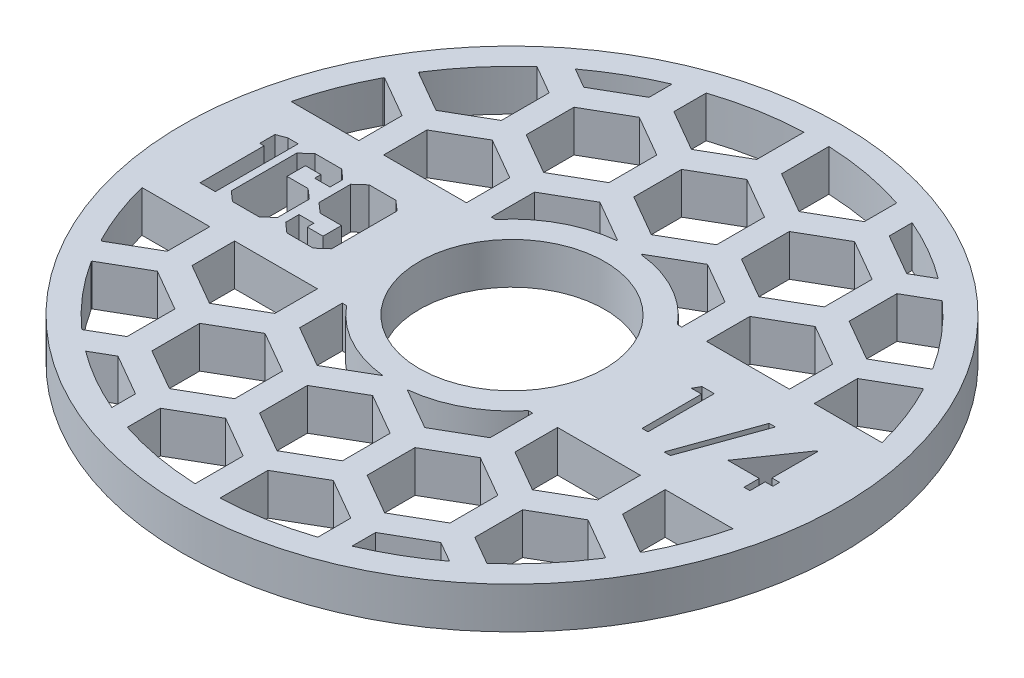
SolidWorks part; units mm, degrees
ref_plane "Front Plane" through (0, 0, 0) normal (0, 0, 1) x (1, 0, 0)
ref_plane "Top Plane" through (0, 0, 0) normal (0, 1, 0) x (1, 0, 0)
ref_plane "Right Plane" through (0, 0, 0) normal (1, 0, 0) x (0, 0, -1)
sketch "Sketch1" plane through (0, 0, 0) normal (0, 1, 0) x (1, 0, 0)
  circle A0 centre (0, 0) radius 14.224
  circle A1 centre (0, 0) radius 50.546
  dimension "D1" = 28.448
  dimension "D2" = 101.092
extrude "Boss-Extrude1" add sketch "Sketch1" along normal blind 6.35
sketch "Sketch2" plane through (0, 6.35, 0) normal (0, 1, 0) x (1, 0, 0)
  line L0 (-14.224, 0) -> (-50.546, 0) construction
  line L1 (-14.224, -6.35) -> (-50.546, -6.35) construction
  line L2 (14.224, 0) -> (50.546, 0) construction
  line L3 (14.224, -5.08) -> (50.546, -5.08) construction
  circle A0 centre (0, 0) radius 14.224 construction
  circle A1 centre (0, 0) radius 50.546 construction
  text T0 "169" font "Jersey M54" height 12.7
  text T1 "1/4" font "Century Gothic" height 10.16
  dimension "D1" = 6.35
  dimension "D2" = 5.08
extrude "Cut-Extrude1" cut sketch "Sketch2" against normal through all both and the other way through all
sketch "Sketch3" plane through (0, 6.35, 0) normal (0, 1, 0) x (1, 0, 0)
  line L0 (0, 11.43) -> (0, -11.43)
  line L1 (-49.2367, 11.43) -> (49.2367, 11.43)
  line L2 (-49.2367, -11.43) -> (49.2367, -11.43)
  line L3 (16.51, -7.3323) -> (22.86, -3.6662)
  line L4 (0, -7.3323) -> (6.35, -3.6662)
  line L5 (6.35, -3.6662) -> (6.35, 3.6662)
  line L6 (6.35, 3.6662) -> (0, 7.3323)
  line L7 (0, 7.3323) -> (-6.35, 3.6662)
  line L8 (-6.35, 3.6662) -> (-6.35, -3.6662)
  line L9 (-6.35, -3.6662) -> (0, -7.3323)
  line L16 (8.255, -21.6304) -> (14.605, -17.9643)
  line L17 (14.605, -17.9643) -> (14.605, -10.6319)
  line L18 (14.605, -10.6319) -> (8.255, -6.9657)
  line L19 (8.255, -6.9657) -> (1.905, -10.6319)
  line L20 (1.905, -10.6319) -> (1.905, -17.9643)
  line L21 (1.905, -17.9643) -> (8.255, -21.6304)
  line L22 (22.86, -3.6662) -> (22.86, 3.6662)
  line L23 (22.86, 3.6662) -> (16.51, 7.3323)
  line L24 (16.51, 7.3323) -> (10.16, 3.6662)
  line L25 (10.16, 3.6662) -> (10.16, -3.6662)
  line L26 (10.16, -3.6662) -> (16.51, -7.3323)
  line L27 (24.765, -21.6304) -> (31.115, -17.9643)
  line L28 (31.115, -17.9643) -> (31.115, -10.6319)
  line L29 (31.115, -10.6319) -> (24.765, -6.9657)
  line L30 (24.765, -6.9657) -> (18.415, -10.6319)
  line L31 (18.415, -10.6319) -> (18.415, -17.9643)
  line L32 (18.415, -17.9643) -> (24.765, -21.6304)
  line L33 (33.02, -7.3323) -> (39.37, -3.6662)
  line L34 (39.37, -3.6662) -> (39.37, 3.6662)
  line L35 (39.37, 3.6662) -> (33.02, 7.3323)
  line L36 (33.02, 7.3323) -> (26.67, 3.6662)
  line L37 (26.67, 3.6662) -> (26.67, -3.6662)
  line L38 (26.67, -3.6662) -> (33.02, -7.3323)
  line L39 (41.275, -21.6304) -> (47.625, -17.9643)
  line L40 (47.625, -17.9643) -> (47.625, -10.6319)
  line L41 (47.625, -10.6319) -> (41.275, -6.9657)
  line L42 (41.275, -6.9657) -> (34.925, -10.6319)
  line L43 (34.925, -10.6319) -> (34.925, -17.9643)
  line L44 (34.925, -17.9643) -> (41.275, -21.6304)
  line L45 (49.53, -7.3323) -> (55.88, -3.6662)
  line L46 (55.88, -3.6662) -> (55.88, 3.6662)
  line L47 (55.88, 3.6662) -> (49.53, 7.3323)
  line L48 (49.53, 7.3323) -> (43.18, 3.6662)
  line L49 (43.18, 3.6662) -> (43.18, -3.6662)
  line L50 (43.18, -3.6662) -> (49.53, -7.3323)
  line L51 (57.785, -21.6304) -> (64.135, -17.9643)
  line L52 (64.135, -17.9643) -> (64.135, -10.6319)
  line L53 (64.135, -10.6319) -> (57.785, -6.9657)
  line L54 (57.785, -6.9657) -> (51.435, -10.6319)
  line L55 (51.435, -10.6319) -> (51.435, -17.9643)
  line L56 (51.435, -17.9643) -> (57.785, -21.6304)
  line L57 (-16.51, -7.3323) -> (-10.16, -3.6662)
  line L58 (-10.16, -3.6662) -> (-10.16, 3.6662)
  line L59 (-10.16, 3.6662) -> (-16.51, 7.3323)
  line L60 (-16.51, 7.3323) -> (-22.86, 3.6662)
  line L61 (-22.86, 3.6662) -> (-22.86, -3.6662)
  line L62 (-22.86, -3.6662) -> (-16.51, -7.3323)
  line L63 (-8.255, -21.6304) -> (-1.905, -17.9643)
  line L64 (-1.905, -17.9643) -> (-1.905, -10.6319)
  line L65 (-1.905, -10.6319) -> (-8.255, -6.9657)
  line L66 (-8.255, -6.9657) -> (-14.605, -10.6319)
  line L67 (-14.605, -10.6319) -> (-14.605, -17.9643)
  line L68 (-14.605, -17.9643) -> (-8.255, -21.6304)
  line L69 (-33.02, -7.3323) -> (-26.67, -3.6662)
  line L70 (-26.67, -3.6662) -> (-26.67, 3.6662)
  line L71 (-26.67, 3.6662) -> (-33.02, 7.3323)
  line L72 (-33.02, 7.3323) -> (-39.37, 3.6662)
  line L73 (-39.37, 3.6662) -> (-39.37, -3.6662)
  line L74 (-39.37, -3.6662) -> (-33.02, -7.3323)
  line L75 (-24.765, -21.6304) -> (-18.415, -17.9643)
  line L76 (-18.415, -17.9643) -> (-18.415, -10.6319)
  line L77 (-18.415, -10.6319) -> (-24.765, -6.9657)
  line L78 (-24.765, -6.9657) -> (-31.115, -10.6319)
  line L79 (-31.115, -10.6319) -> (-31.115, -17.9643)
  line L80 (-31.115, -17.9643) -> (-24.765, -21.6304)
  line L81 (-49.53, -7.3323) -> (-43.18, -3.6662)
  line L82 (-43.18, -3.6662) -> (-43.18, 3.6662)
  line L83 (-43.18, 3.6662) -> (-49.53, 7.3323)
  line L84 (-49.53, 7.3323) -> (-55.88, 3.6662)
  line L85 (-55.88, 3.6662) -> (-55.88, -3.6662)
  line L86 (-55.88, -3.6662) -> (-49.53, -7.3323)
  line L87 (-41.275, -21.6304) -> (-34.925, -17.9643)
  line L88 (-34.925, -17.9643) -> (-34.925, -10.6319)
  line L89 (-34.925, -10.6319) -> (-41.275, -6.9657)
  line L90 (-41.275, -6.9657) -> (-47.625, -10.6319)
  line L91 (-47.625, -10.6319) -> (-47.625, -17.9643)
  line L92 (-47.625, -17.9643) -> (-41.275, -21.6304)
  line L93 (-49.53, 21.3697) -> (-43.18, 25.0358)
  line L94 (-43.18, 25.0358) -> (-43.18, 32.3682)
  line L95 (-43.18, 32.3682) -> (-49.53, 36.0343)
  line L96 (-49.53, 36.0343) -> (-55.88, 32.3682)
  line L97 (-55.88, 32.3682) -> (-55.88, 25.0358)
  line L98 (-55.88, 25.0358) -> (-49.53, 21.3697)
  line L99 (-41.275, 7.0716) -> (-34.925, 10.7377)
  line L100 (-34.925, 10.7377) -> (-34.925, 18.0701)
  line L101 (-34.925, 18.0701) -> (-41.275, 21.7363)
  line L102 (-41.275, 21.7363) -> (-47.625, 18.0701)
  line L103 (-47.625, 18.0701) -> (-47.625, 10.7377)
  line L104 (-47.625, 10.7377) -> (-41.275, 7.0716)
  line L105 (-33.02, 21.3697) -> (-26.67, 25.0358)
  line L106 (-26.67, 25.0358) -> (-26.67, 32.3682)
  line L107 (-26.67, 32.3682) -> (-33.02, 36.0343)
  line L108 (-33.02, 36.0343) -> (-39.37, 32.3682)
  line L109 (-39.37, 32.3682) -> (-39.37, 25.0358)
  line L110 (-39.37, 25.0358) -> (-33.02, 21.3697)
  line L111 (-24.765, 7.0716) -> (-18.415, 10.7377)
  line L112 (-18.415, 10.7377) -> (-18.415, 18.0701)
  line L113 (-18.415, 18.0701) -> (-24.765, 21.7363)
  line L114 (-24.765, 21.7363) -> (-31.115, 18.0701)
  line L115 (-31.115, 18.0701) -> (-31.115, 10.7377)
  line L116 (-31.115, 10.7377) -> (-24.765, 7.0716)
  line L117 (-16.51, 21.3697) -> (-10.16, 25.0358)
  line L118 (-10.16, 25.0358) -> (-10.16, 32.3682)
  line L119 (-10.16, 32.3682) -> (-16.51, 36.0343)
  line L120 (-16.51, 36.0343) -> (-22.86, 32.3682)
  line L121 (-22.86, 32.3682) -> (-22.86, 25.0358)
  line L122 (-22.86, 25.0358) -> (-16.51, 21.3697)
  line L123 (-8.255, 7.0716) -> (-1.905, 10.7377)
  line L124 (-1.905, 10.7377) -> (-1.905, 18.0701)
  line L125 (-1.905, 18.0701) -> (-8.255, 21.7363)
  line L126 (-8.255, 21.7363) -> (-14.605, 18.0701)
  line L127 (-14.605, 18.0701) -> (-14.605, 10.7377)
  line L128 (-14.605, 10.7377) -> (-8.255, 7.0716)
  line L129 (0, 21.3697) -> (6.35, 25.0358)
  line L130 (6.35, 25.0358) -> (6.35, 32.3682)
  line L131 (6.35, 32.3682) -> (0, 36.0343)
  line L132 (0, 36.0343) -> (-6.35, 32.3682)
  line L133 (-6.35, 32.3682) -> (-6.35, 25.0358)
  line L134 (-6.35, 25.0358) -> (0, 21.3697)
  line L135 (8.255, 7.0716) -> (14.605, 10.7377)
  line L136 (14.605, 10.7377) -> (14.605, 18.0701)
  line L137 (14.605, 18.0701) -> (8.255, 21.7363)
  line L138 (8.255, 21.7363) -> (1.905, 18.0701)
  line L139 (1.905, 18.0701) -> (1.905, 10.7377)
  line L140 (1.905, 10.7377) -> (8.255, 7.0716)
  line L141 (16.51, 21.3697) -> (22.86, 25.0358)
  line L142 (22.86, 25.0358) -> (22.86, 32.3682)
  line L143 (22.86, 32.3682) -> (16.51, 36.0343)
  line L144 (16.51, 36.0343) -> (10.16, 32.3682)
  line L145 (10.16, 32.3682) -> (10.16, 25.0358)
  line L146 (10.16, 25.0358) -> (16.51, 21.3697)
  line L147 (24.765, 7.0716) -> (31.115, 10.7377)
  line L148 (31.115, 10.7377) -> (31.115, 18.0701)
  line L149 (31.115, 18.0701) -> (24.765, 21.7363)
  line L150 (24.765, 21.7363) -> (18.415, 18.0701)
  line L151 (18.415, 18.0701) -> (18.415, 10.7377)
  line L152 (18.415, 10.7377) -> (24.765, 7.0716)
  line L153 (33.02, 21.3697) -> (39.37, 25.0358)
  line L154 (39.37, 25.0358) -> (39.37, 32.3682)
  line L155 (39.37, 32.3682) -> (33.02, 36.0343)
  line L156 (33.02, 36.0343) -> (26.67, 32.3682)
  line L157 (26.67, 32.3682) -> (26.67, 25.0358)
  line L158 (26.67, 25.0358) -> (33.02, 21.3697)
  line L159 (41.275, 7.0716) -> (47.625, 10.7377)
  line L160 (47.625, 10.7377) -> (47.625, 18.0701)
  line L161 (47.625, 18.0701) -> (41.275, 21.7363)
  line L162 (41.275, 21.7363) -> (34.925, 18.0701)
  line L163 (34.925, 18.0701) -> (34.925, 10.7377)
  line L164 (34.925, 10.7377) -> (41.275, 7.0716)
  line L165 (49.53, 21.3697) -> (55.88, 25.0358)
  line L166 (55.88, 25.0358) -> (55.88, 32.3682)
  line L167 (55.88, 32.3682) -> (49.53, 36.0343)
  line L168 (49.53, 36.0343) -> (43.18, 32.3682)
  line L169 (43.18, 32.3682) -> (43.18, 25.0358)
  line L170 (43.18, 25.0358) -> (49.53, 21.3697)
  line L171 (57.785, 7.0716) -> (64.135, 10.7377)
  line L172 (64.135, 10.7377) -> (64.135, 18.0701)
  line L173 (64.135, 18.0701) -> (57.785, 21.7363)
  line L174 (57.785, 21.7363) -> (51.435, 18.0701)
  line L175 (51.435, 18.0701) -> (51.435, 10.7377)
  line L176 (51.435, 10.7377) -> (57.785, 7.0716)
  line L177 (-49.53, 50.0717) -> (-43.18, 53.7378)
  line L178 (-43.18, 53.7378) -> (-43.18, 61.0702)
  line L179 (-43.18, 61.0702) -> (-49.53, 64.7363)
  line L180 (-49.53, 64.7363) -> (-55.88, 61.0702)
  line L181 (-55.88, 61.0702) -> (-55.88, 53.7378)
  line L182 (-55.88, 53.7378) -> (-49.53, 50.0717)
  line L183 (-41.275, 35.7736) -> (-34.925, 39.4397)
  line L184 (-34.925, 39.4397) -> (-34.925, 46.7721)
  line L185 (-34.925, 46.7721) -> (-41.275, 50.4383)
  line L186 (-41.275, 50.4383) -> (-47.625, 46.7721)
  line L187 (-47.625, 46.7721) -> (-47.625, 39.4397)
  line L188 (-47.625, 39.4397) -> (-41.275, 35.7736)
  line L189 (-33.02, 50.0717) -> (-26.67, 53.7378)
  line L190 (-26.67, 53.7378) -> (-26.67, 61.0702)
  line L191 (-26.67, 61.0702) -> (-33.02, 64.7363)
  line L192 (-33.02, 64.7363) -> (-39.37, 61.0702)
  line L193 (-39.37, 61.0702) -> (-39.37, 53.7378)
  line L194 (-39.37, 53.7378) -> (-33.02, 50.0717)
  line L195 (-24.765, 35.7736) -> (-18.415, 39.4397)
  line L196 (-18.415, 39.4397) -> (-18.415, 46.7721)
  line L197 (-18.415, 46.7721) -> (-24.765, 50.4383)
  line L198 (-24.765, 50.4383) -> (-31.115, 46.7721)
  line L199 (-31.115, 46.7721) -> (-31.115, 39.4397)
  line L200 (-31.115, 39.4397) -> (-24.765, 35.7736)
  line L201 (-16.51, 50.0717) -> (-10.16, 53.7378)
  line L202 (-10.16, 53.7378) -> (-10.16, 61.0702)
  line L203 (-10.16, 61.0702) -> (-16.51, 64.7363)
  line L204 (-16.51, 64.7363) -> (-22.86, 61.0702)
  line L205 (-22.86, 61.0702) -> (-22.86, 53.7378)
  line L206 (-22.86, 53.7378) -> (-16.51, 50.0717)
  line L207 (-8.255, 35.7736) -> (-1.905, 39.4397)
  line L208 (-1.905, 39.4397) -> (-1.905, 46.7721)
  line L209 (-1.905, 46.7721) -> (-8.255, 50.4383)
  line L210 (-8.255, 50.4383) -> (-14.605, 46.7721)
  line L211 (-14.605, 46.7721) -> (-14.605, 39.4397)
  line L212 (-14.605, 39.4397) -> (-8.255, 35.7736)
  line L213 (0, 50.0717) -> (6.35, 53.7378)
  line L214 (6.35, 53.7378) -> (6.35, 61.0702)
  line L215 (6.35, 61.0702) -> (0, 64.7363)
  line L216 (0, 64.7363) -> (-6.35, 61.0702)
  line L217 (-6.35, 61.0702) -> (-6.35, 53.7378)
  line L218 (-6.35, 53.7378) -> (0, 50.0717)
  line L219 (8.255, 35.7736) -> (14.605, 39.4397)
  line L220 (14.605, 39.4397) -> (14.605, 46.7721)
  line L221 (14.605, 46.7721) -> (8.255, 50.4383)
  line L222 (8.255, 50.4383) -> (1.905, 46.7721)
  line L223 (1.905, 46.7721) -> (1.905, 39.4397)
  line L224 (1.905, 39.4397) -> (8.255, 35.7736)
  line L225 (16.51, 50.0717) -> (22.86, 53.7378)
  line L226 (22.86, 53.7378) -> (22.86, 61.0702)
  line L227 (22.86, 61.0702) -> (16.51, 64.7363)
  line L228 (16.51, 64.7363) -> (10.16, 61.0702)
  line L229 (10.16, 61.0702) -> (10.16, 53.7378)
  line L230 (10.16, 53.7378) -> (16.51, 50.0717)
  line L231 (24.765, 35.7736) -> (31.115, 39.4397)
  line L232 (31.115, 39.4397) -> (31.115, 46.7721)
  line L233 (31.115, 46.7721) -> (24.765, 50.4383)
  line L234 (24.765, 50.4383) -> (18.415, 46.7721)
  line L235 (18.415, 46.7721) -> (18.415, 39.4397)
  line L236 (18.415, 39.4397) -> (24.765, 35.7736)
  line L237 (33.02, 50.0717) -> (39.37, 53.7378)
  line L238 (39.37, 53.7378) -> (39.37, 61.0702)
  line L239 (39.37, 61.0702) -> (33.02, 64.7363)
  line L240 (33.02, 64.7363) -> (26.67, 61.0702)
  line L241 (26.67, 61.0702) -> (26.67, 53.7378)
  line L242 (26.67, 53.7378) -> (33.02, 50.0717)
  line L243 (41.275, 35.7736) -> (47.625, 39.4397)
  line L244 (47.625, 39.4397) -> (47.625, 46.7721)
  line L245 (47.625, 46.7721) -> (41.275, 50.4383)
  line L246 (41.275, 50.4383) -> (34.925, 46.7721)
  line L247 (34.925, 46.7721) -> (34.925, 39.4397)
  line L248 (34.925, 39.4397) -> (41.275, 35.7736)
  line L249 (49.53, 50.0717) -> (55.88, 53.7378)
  line L250 (55.88, 53.7378) -> (55.88, 61.0702)
  line L251 (55.88, 61.0702) -> (49.53, 64.7363)
  line L252 (49.53, 64.7363) -> (43.18, 61.0702)
  line L253 (43.18, 61.0702) -> (43.18, 53.7378)
  line L254 (43.18, 53.7378) -> (49.53, 50.0717)
  line L255 (57.785, 35.7736) -> (64.135, 39.4397)
  line L256 (64.135, 39.4397) -> (64.135, 46.7721)
  line L257 (64.135, 46.7721) -> (57.785, 50.4383)
  line L258 (57.785, 50.4383) -> (51.435, 46.7721)
  line L259 (51.435, 46.7721) -> (51.435, 39.4397)
  line L260 (51.435, 39.4397) -> (57.785, 35.7736)
  line L261 (-49.53, -36.0343) -> (-43.18, -32.3682)
  line L262 (-43.18, -32.3682) -> (-43.18, -25.0358)
  line L263 (-43.18, -25.0358) -> (-49.53, -21.3697)
  line L264 (-49.53, -21.3697) -> (-55.88, -25.0358)
  line L265 (-55.88, -25.0358) -> (-55.88, -32.3682)
  line L266 (-55.88, -32.3682) -> (-49.53, -36.0343)
  line L267 (-41.275, -50.3324) -> (-34.925, -46.6663)
  line L268 (-34.925, -46.6663) -> (-34.925, -39.3339)
  line L269 (-34.925, -39.3339) -> (-41.275, -35.6677)
  line L270 (-41.275, -35.6677) -> (-47.625, -39.3339)
  line L271 (-47.625, -39.3339) -> (-47.625, -46.6663)
  line L272 (-47.625, -46.6663) -> (-41.275, -50.3324)
  line L273 (-33.02, -36.0343) -> (-26.67, -32.3682)
  line L274 (-26.67, -32.3682) -> (-26.67, -25.0358)
  line L275 (-26.67, -25.0358) -> (-33.02, -21.3697)
  line L276 (-33.02, -21.3697) -> (-39.37, -25.0358)
  line L277 (-39.37, -25.0358) -> (-39.37, -32.3682)
  line L278 (-39.37, -32.3682) -> (-33.02, -36.0343)
  line L279 (-24.765, -50.3324) -> (-18.415, -46.6663)
  line L280 (-18.415, -46.6663) -> (-18.415, -39.3339)
  line L281 (-18.415, -39.3339) -> (-24.765, -35.6677)
  line L282 (-24.765, -35.6677) -> (-31.115, -39.3339)
  line L283 (-31.115, -39.3339) -> (-31.115, -46.6663)
  line L284 (-31.115, -46.6663) -> (-24.765, -50.3324)
  line L285 (-16.51, -36.0343) -> (-10.16, -32.3682)
  line L286 (-10.16, -32.3682) -> (-10.16, -25.0358)
  line L287 (-10.16, -25.0358) -> (-16.51, -21.3697)
  line L288 (-16.51, -21.3697) -> (-22.86, -25.0358)
  line L289 (-22.86, -25.0358) -> (-22.86, -32.3682)
  line L290 (-22.86, -32.3682) -> (-16.51, -36.0343)
  line L291 (-8.255, -50.3324) -> (-1.905, -46.6663)
  line L292 (-1.905, -46.6663) -> (-1.905, -39.3339)
  line L293 (-1.905, -39.3339) -> (-8.255, -35.6677)
  line L294 (-8.255, -35.6677) -> (-14.605, -39.3339)
  line L295 (-14.605, -39.3339) -> (-14.605, -46.6663)
  line L296 (-14.605, -46.6663) -> (-8.255, -50.3324)
  line L297 (0, -36.0343) -> (6.35, -32.3682)
  line L298 (6.35, -32.3682) -> (6.35, -25.0358)
  line L299 (6.35, -25.0358) -> (0, -21.3697)
  line L300 (0, -21.3697) -> (-6.35, -25.0358)
  line L301 (-6.35, -25.0358) -> (-6.35, -32.3682)
  line L302 (-6.35, -32.3682) -> (0, -36.0343)
  line L303 (8.255, -50.3324) -> (14.605, -46.6663)
  line L304 (14.605, -46.6663) -> (14.605, -39.3339)
  line L305 (14.605, -39.3339) -> (8.255, -35.6677)
  line L306 (8.255, -35.6677) -> (1.905, -39.3339)
  line L307 (1.905, -39.3339) -> (1.905, -46.6663)
  line L308 (1.905, -46.6663) -> (8.255, -50.3324)
  line L309 (16.51, -36.0343) -> (22.86, -32.3682)
  line L310 (22.86, -32.3682) -> (22.86, -25.0358)
  line L311 (22.86, -25.0358) -> (16.51, -21.3697)
  line L312 (16.51, -21.3697) -> (10.16, -25.0358)
  line L313 (10.16, -25.0358) -> (10.16, -32.3682)
  line L314 (10.16, -32.3682) -> (16.51, -36.0343)
  line L315 (24.765, -50.3324) -> (31.115, -46.6663)
  line L316 (31.115, -46.6663) -> (31.115, -39.3339)
  line L317 (31.115, -39.3339) -> (24.765, -35.6677)
  line L318 (24.765, -35.6677) -> (18.415, -39.3339)
  line L319 (18.415, -39.3339) -> (18.415, -46.6663)
  line L320 (18.415, -46.6663) -> (24.765, -50.3324)
  line L321 (33.02, -36.0343) -> (39.37, -32.3682)
  line L322 (39.37, -32.3682) -> (39.37, -25.0358)
  line L323 (39.37, -25.0358) -> (33.02, -21.3697)
  line L324 (33.02, -21.3697) -> (26.67, -25.0358)
  line L325 (26.67, -25.0358) -> (26.67, -32.3682)
  line L326 (26.67, -32.3682) -> (33.02, -36.0343)
  line L327 (41.275, -50.3324) -> (47.625, -46.6663)
  line L328 (47.625, -46.6663) -> (47.625, -39.3339)
  line L329 (47.625, -39.3339) -> (41.275, -35.6677)
  line L330 (41.275, -35.6677) -> (34.925, -39.3339)
  line L331 (34.925, -39.3339) -> (34.925, -46.6663)
  line L332 (34.925, -46.6663) -> (41.275, -50.3324)
  line L333 (49.53, -36.0343) -> (55.88, -32.3682)
  line L334 (55.88, -32.3682) -> (55.88, -25.0358)
  line L335 (55.88, -25.0358) -> (49.53, -21.3697)
  line L336 (49.53, -21.3697) -> (43.18, -25.0358)
  line L337 (43.18, -25.0358) -> (43.18, -32.3682)
  line L338 (43.18, -32.3682) -> (49.53, -36.0343)
  line L339 (57.785, -50.3324) -> (64.135, -46.6663)
  line L340 (64.135, -46.6663) -> (64.135, -39.3339)
  line L341 (64.135, -39.3339) -> (57.785, -35.6677)
  line L342 (57.785, -35.6677) -> (51.435, -39.3339)
  line L343 (51.435, -39.3339) -> (51.435, -46.6663)
  line L344 (51.435, -46.6663) -> (57.785, -50.3324)
  circle A0 centre (0, 0) radius 50.546 construction
  circle A1 centre (0, 0) radius 18.034
  circle A2 centre (0, 0) radius 46.736
  circle A3 centre (0, 0) radius 6.35 construction
  circle A4 centre (8.255, -14.2981) radius 6.35 construction
  point P4 (0, 0)
  point P10 (0, 11.43)
  point P13 (0, -11.43)
  dimension "D2" = 36.068
  dimension "D3" = 93.472
  dimension "D1" = 22.86
  dimension "D4" = 12.7
  dimension "D5" = 12.7
  dimension "D6" = 3.81
  dimension "D7" = 1.905
  dimension "D8" = 4
  dimension "D9" = 4
  dimension "D10" = 3
  dimension "D11" = 2
extrude "Cut-Extrude2" cut sketch "Sketch3" against normal through all both and the other way through all contours L102 A2 L1 L100 L101 | L114 L115 L1 L112 L113 | L107 A2 L109 L110 L105 L106 | L196 A2 L200 L195 | L121 L122 L117 L118 L119 L120 | L208 A2 L211 L212 L207 | L133 L134 L129 L130 L131 L132 | L220 A2 L223 L224 L219 | A1 L124 L125 L126 L127 L1 | A1 L1 L136 L137 L138 L139 | L145 L146 L141 L142 L143 L144 | L231 A2 L235 L236 | L154 A2 L156 L157 L158 L153 | L150 L151 L1 L148 L149 | L1 A2 L161 L162 L163 | L39 A2 L2 L43 L44 | L31 L32 L27 L28 L2 | L326 A2 L322 L323 L324 L325 | L313 L314 L309 L310 L311 L312 | A1 L20 L21 L16 L17 L2 | L301 L302 L297 L298 L299 L300 | L319 A2 L317 L318 | L308 A2 L304 L305 L306 L307 | L295 A2 L291 L292 L293 L294 | L282 A2 L280 L281 | L289 L290 L285 L286 L287 L288 | L277 A2 L273 L274 L275 L276 | L2 A2 L92 L87 L88 | L79 L80 L75 L76 L2 | A1 L2 L67 L68 L63 L64
